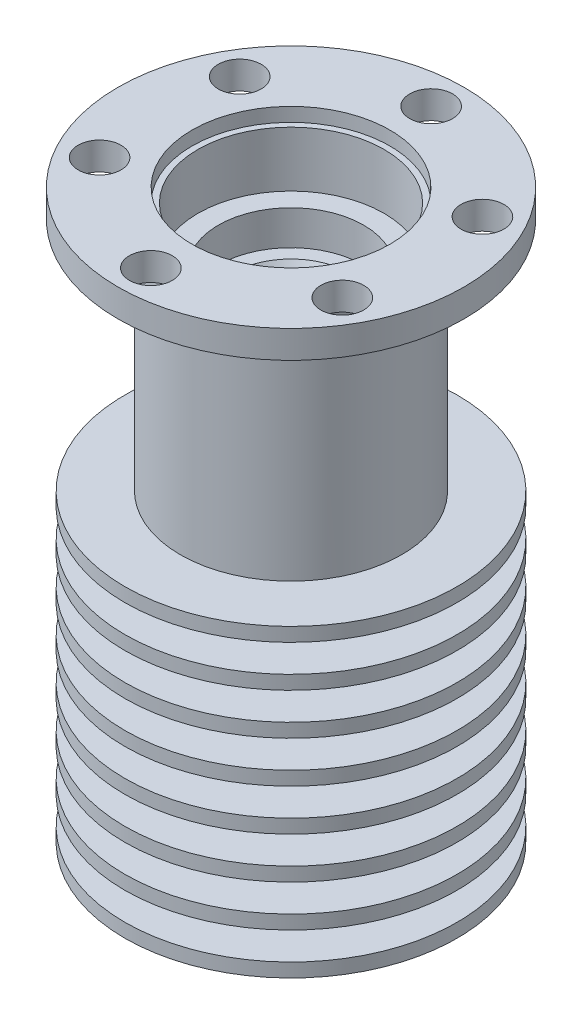
SolidWorks part; units mm, degrees
material "aluminio"
ref_plane "Alzado" through (0, 0, 0) normal (0, 0, 1) x (1, 0, 0)
ref_plane "Planta" through (0, 0, 0) normal (0, 1, 0) x (1, 0, 0)
ref_plane "Vista lateral" through (0, 0, 0) normal (1, 0, 0) x (0, 0, -1)
sketch "Croquis1" plane through (0, 0, 0) normal (0, 0, 1) x (1, 0, 0)
  line L0 (0, 0) -> (6, 0)
  line L1 (6, 0) -> (6, 9)
  line L2 (6, 9) -> (5.25, 9)
  line L3 (5.25, 9) -> (5.25, 12)
  line L4 (5.25, 12) -> (4.75, 12)
  line L5 (4.75, 12) -> (4.75, 22)
  line L6 (8, 39) -> (12.5, 39)
  line L7 (0, 41) -> (0, 0)
  line L8 (12.5, 39) -> (12.5, 41)
  line L9 (12.5, 41) -> (0, 41)
  line L12 (4.75, 22) -> (8, 22)
  line L13 (8, 22) -> (8, 39)
  line L19 (0, 41) -> (0, 0) construction
  dimension "D1" = 9
  dimension "D2" = 3
  dimension "D3" = 10
  dimension "D4" = 2
  dimension "D5" = 12.5
  dimension "D7" = 17
  dimension "D8" = 6
  dimension "D9" = 5.25
  dimension "D10" = 4.75
  dimension "D14" = 8
revolve "Revolución1" add sketch "Croquis1" angle 360 about L19
sketch "Croquis2" plane through (0, 0, 0) normal (0, 0, 1) x (1, 0, 0)
  line L0 (0, 0) -> (0, 41) construction
  line L2 (0, 0) -> (2.5, 0)
  line L3 (2.5, 0) -> (2.5, 12)
  line L4 (2.5, 12) -> (1.7, 12)
  line L5 (1.7, 12) -> (1.7, 14)
  line L6 (1.7, 14) -> (3.25, 14)
  line L7 (3.25, 14) -> (3.25, 33.5)
  line L8 (3.25, 33.5) -> (5.25, 33.5)
  line L9 (5.25, 33.5) -> (5.25, 36)
  line L10 (12.5, 41) -> (-12.5, 41) construction
  line L11 (0, 41) -> (6.725, 41)
  line L12 (5.25, 36) -> (6.725, 36)
  line L13 (6.725, 36) -> (6.725, 41)
  line L14 (0, 41) -> (0, 0)
  dimension "D1" = 12
  dimension "D2" = 2
  dimension "D3" = 5
  dimension "D5" = 2.5
  dimension "D6" = 13.45
  dimension "D8" = 10.5
  dimension "D9" = 6.5
  dimension "D10" = 3.4
  dimension "D11" = 5
revolve "Cortar-Revolución1" cut sketch "Croquis2" angle 360 about L0
cosmetic thread "Rosca cosmética1" parameters "D1"=10, "D2"=6
sketch "Croquis3" plane through (0, 0, 0) normal (0, -1, 0) x (1, 0, 0)
  circle A0 centre (0, 0) radius 3.25
  circle A1 centre (0, 0) radius 12
  dimension "D1" = 24
  dimension "D2" = 6.5
extrude "Saliente-Extruir1" add sketch "Croquis3" against normal blind 1
sketch "Croquis4" plane through (0, 0, 0) normal (0, 0, 1) x (1, 0, 0)
  line L0 (0, 0) -> (0, 36.9563) construction
pattern_linear "MatrizL1" count 8 spacing 3 along (0, 1, 0) of "Saliente-Extruir1"
sketch "Croquis5" plane through (0, 41, 0) normal (0, 1, 0) x (1, 0, 0)
  circle A0 centre (0, 0) radius 10.125 construction
  circle A1 centre (0, 10.125) radius 1.55
  dimension "D1" = 20.25
  dimension "D2" = 3.1
extrude "Cortar-Extruir1" cut sketch "Croquis5" against normal up to next (2 mm away)
pattern_circular "MatrizC1" count 6 over 360 about axis through (0, 0, 0) along (0, 1, 0) of "Cortar-Extruir1"
chamfer "Chaflán3" distance 0.3 angle 60 1 edges at (0, 14, -1.7)
sketch "Croquis6" plane through (0, 41, 0) normal (0, 1, 0) x (1, 0, 0)
  circle A0 centre (0, 0) radius 7.15
  dimension "D1" = 14.3
extrude "Cortar-Extruir2" cut sketch "Croquis6" against normal blind 1
chamfer "Chaflán2" distance 0.15 angle 60 1 edges at (0, 12, -1.7)
chamfer "Chaflán4" distance 1 angle 60 1 edges at (0, 33.5, -3.25)
